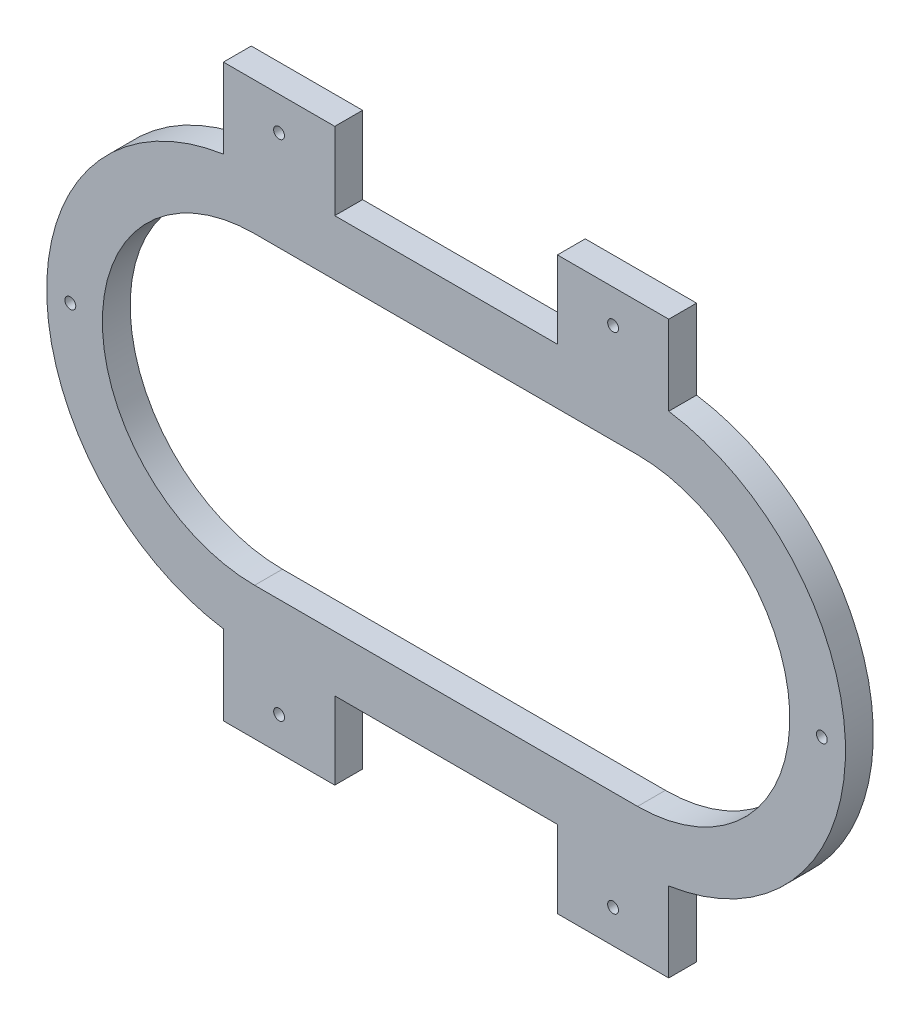
SolidWorks part; units mm, degrees
ref_plane "Front Plane" through (0, 0, 0) normal (0, 0, 1) x (1, 0, 0)
ref_plane "Top Plane" through (0, 0, 0) normal (0, 1, 0) x (1, 0, 0)
ref_plane "Right Plane" through (0, 0, 0) normal (1, 0, 0) x (0, 0, -1)
sketch "Sketch1" plane through (0, 0, 0) normal (0, 0, 1) x (1, 0, 0)
  line L0 (-70.1549, 6.368) -> (67.4451, 6.368) construction
  line L1 (-70.1549, 61.068) -> (67.4451, 61.068)
  line L2 (-70.1549, -48.332) -> (67.4451, -48.332)
  line L3 (-70.1549, 81.068) -> (67.4451, 81.068)
  line L4 (-70.1549, -68.332) -> (67.4451, -68.332)
  line L5 (-81.3549, -67.4876) -> (-81.3549, -88.8406)
  line L6 (-41.3549, -96.132) -> (-81.3549, -96.132)
  line L7 (-41.3549, -68.332) -> (-41.3549, -96.132)
  line L8 (-81.3549, -88.8406) -> (-81.3549, -96.132)
  line L9 (38.6451, -68.332) -> (38.6451, -96.132)
  line L10 (38.6451, -96.132) -> (78.6451, -96.132)
  line L11 (78.6451, -96.132) -> (78.6451, -67.4876)
  line L12 (-41.3549, 81.068) -> (-41.3549, 108.868)
  line L13 (-41.3549, 108.868) -> (-81.3549, 108.868)
  line L14 (-81.3549, 108.868) -> (-81.3549, 80.2236)
  line L15 (38.6451, 81.068) -> (38.6451, 108.868)
  line L16 (38.6451, 108.868) -> (78.6451, 108.868)
  line L17 (78.6451, 108.868) -> (78.6451, 80.2236)
  line L30 (-81.3549, 88.868) -> (-41.3549, 88.868)
  line L31 (38.6451, 88.868) -> (78.6451, 88.868)
  line L32 (-81.3549, -76.132) -> (-41.3549, -76.132)
  line L33 (38.6451, -76.132) -> (78.6451, -76.132)
  line L34 (-41.3549, 81.068) -> (-41.3549, 78.068)
  line L35 (-41.3549, 78.068) -> (-81.3549, 78.068)
  line L36 (-81.3549, 78.068) -> (-81.3549, 80.2236)
  line L37 (38.6451, 81.068) -> (38.6451, 78.068)
  line L38 (38.6451, 78.068) -> (78.6451, 78.068)
  line L39 (78.6451, 78.068) -> (78.6451, 80.2236)
  line L40 (-41.3549, -68.332) -> (-41.3549, -65.332)
  line L41 (-41.3549, -65.332) -> (-81.3549, -65.332)
  line L42 (-81.3549, -65.332) -> (-81.3549, -67.4876)
  line L43 (38.6451, -68.332) -> (38.6451, -65.332)
  line L44 (38.6451, -65.332) -> (78.6451, -65.332)
  line L45 (78.6451, -65.332) -> (78.6451, -67.4876)
  arc A0 (-70.1549, 61.068) -> (-70.1549, -48.332) centre (-70.1549, 6.368) ccw
  arc A1 (67.4451, -48.332) -> (67.4451, 61.068) centre (67.4451, 6.368) ccw
  arc A2 (67.4451, -68.332) -> (67.4451, 81.068) centre (67.4451, 6.368) ccw
  arc A3 (-70.1549, 81.068) -> (-70.1549, -68.332) centre (-70.1549, 6.368) ccw
  circle A4 centre (-61.3549, 96.868) radius 1.95
  circle A5 centre (58.6451, 96.868) radius 1.95
  circle A6 centre (-61.3549, -84.132) radius 1.95
  circle A7 centre (58.6451, -84.132) radius 1.95
  circle A8 centre (133.6451, 6.368) radius 1.95
  circle A9 centre (-136.3549, 6.368) radius 1.95
  point P2 (-1.3549, 6.368)
  point P7 (-124.8549, 6.368)
  point P8 (122.1451, 6.368)
  point P15 (-1.3549, 61.068)
  point P16 (-1.3549, 81.068)
  point P17 (38.6451, 81.068)
  point P18 (78.6451, 81.068)
  point P19 (78.6451, 80.2236)
  point P20 (-41.3549, 81.068)
  point P21 (-41.3549, 61.068)
  point P22 (-1.3549, -48.332)
  point P23 (-1.3549, -68.332)
  point P24 (-35.3445, -48.332)
  point P25 (-41.3549, -68.332)
  point P26 (-54.0554, -48.332)
  point P27 (-81.3549, -68.332)
  point P28 (21.6322, -48.332)
  point P29 (38.6451, -68.332)
  point P30 (41.1872, -48.332)
  point P31 (78.6451, -68.332)
  point P32 (-81.3549, 81.068)
  point P33 (-56.6064, 61.068)
  point P34 (-81.3549, -67.4876)
  point P35 (78.6451, -67.4876)
  point P36 (-81.3549, 80.2236)
  point P62 (-81.3549, 88.868)
  point P63 (-41.3549, 88.868)
  point P68 (38.6451, 88.868)
  point P69 (78.6451, 88.868)
  point P71 (-144.8549, 6.368)
  point P74 (-41.3549, -76.132)
  point P75 (-81.3549, -76.132)
  point P80 (38.6451, -76.132)
  point P81 (78.6451, -76.132)
  point P87 (142.1451, 6.368)
  dimension "D1" = 54.7
  dimension "D18" = 3.9
  dimension "D23" = 3.9
  dimension "D28" = 3.9
  dimension "D33" = 3.9
  dimension "D42" = 3.9
  dimension "D44" = 3.9
  dimension "D2" = 20
  dimension "D3" = 40
  dimension "D4" = 20
  dimension "D5" = 40
  dimension "D6" = 40
  dimension "D7" = 40
  dimension "D8" = 40
  dimension "D9" = 40
  dimension "D10" = 40
  dimension "D11" = 40
  dimension "D12" = 27.8
  dimension "D13" = 27.8
  dimension "D14" = 27.8
  dimension "D15" = 27.8
  dimension "D16" = 20
  dimension "D17" = 20
  dimension "D19" = 8
  dimension "D20" = 20
  dimension "D21" = 20
  dimension "D22" = 8
  dimension "D24" = 40
  dimension "D25" = 20
  dimension "D26" = 20
  dimension "D27" = 20
  dimension "D29" = 8
  dimension "D30" = 20
  dimension "D31" = 20
  dimension "D32" = 20
  dimension "D34" = 8
  dimension "D35" = 20
  dimension "D36" = 3
  dimension "D37" = 3
  dimension "D38" = 27.8
  dimension "D39" = 40
  dimension "D40" = 40
  dimension "D41" = 40
  dimension "D43" = 8.5
  dimension "D45" = 8.5
extrude "Boss-Extrude1" add sketch "Sketch1" along normal blind 10
